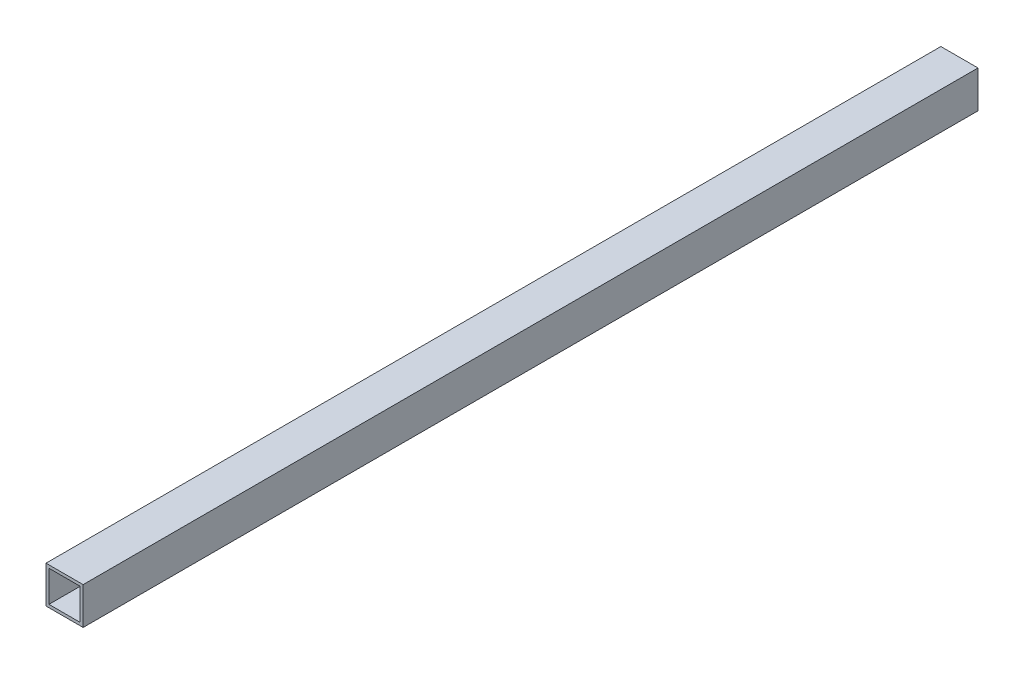
SolidWorks part; units mm, degrees
ref_plane "Front Plane" through (0, 0, 0) normal (0, 0, 1) x (1, 0, 0)
ref_plane "Top Plane" through (0, 0, 0) normal (0, 1, 0) x (1, 0, 0)
ref_plane "Right Plane" through (0, 0, 0) normal (1, 0, 0) x (0, 0, -1)
sketch "Sketch1" plane through (0, 0, 0) normal (0, 0, 1) x (1, 0, 0)
  line L0 (-10.7, 10.7) -> (10.7, 10.7)
  line L1 (-12.7, -12.7) -> (12.7, -12.7)
  line L2 (-12.7, -12.7) -> (-12.7, 12.7)
  line L3 (-12.7, 12.7) -> (12.7, 12.7)
  line L4 (12.7, -12.7) -> (12.7, 12.7)
  line L5 (-12.7, -12.7) -> (12.7, 12.7) construction
  line L6 (-12.7, 12.7) -> (12.7, -12.7) construction
  line L7 (10.7, -10.7) -> (10.7, 10.7)
  line L8 (-10.7, -10.7) -> (10.7, -10.7)
  line L9 (-10.7, -10.7) -> (-10.7, 10.7)
  point P0 (0, 0)
  dimension "D1" = 25.4
  dimension "D2" = 2
extrude "Boss-Extrude1" add sketch "Sketch1" along normal blind 612
